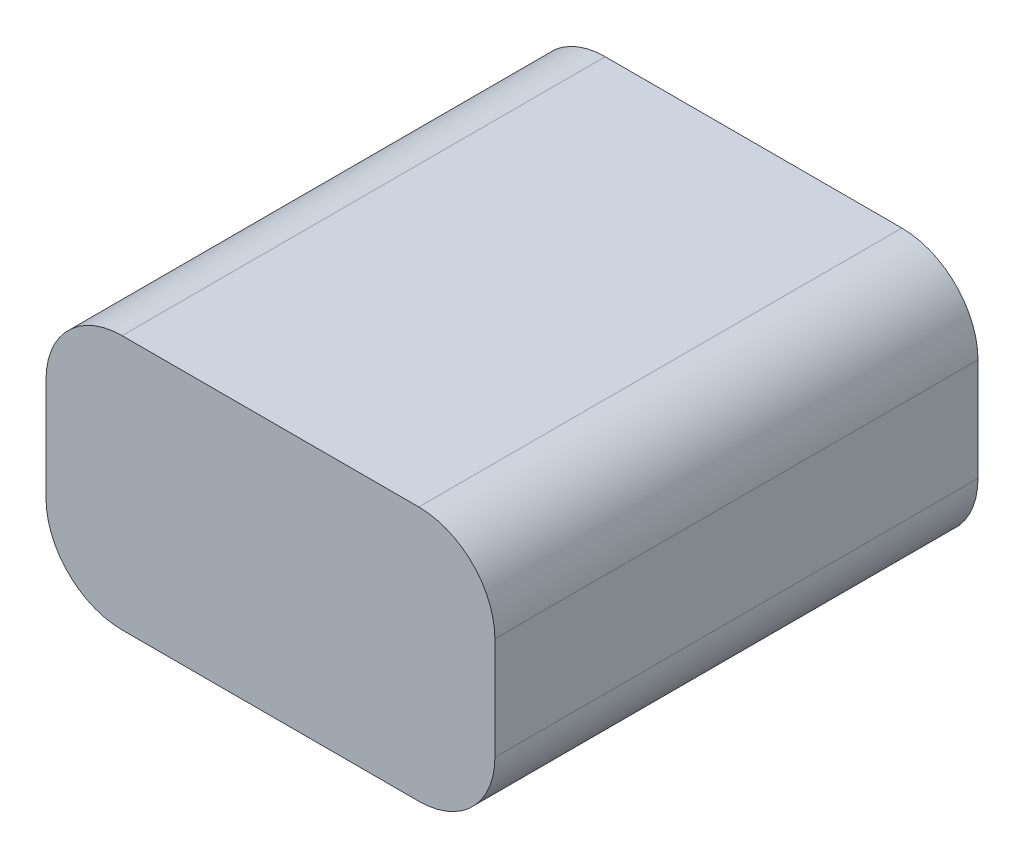
SolidWorks part; units mm, degrees
ref_plane "Front Plane" through (0, 0, 0) normal (0, 0, 1) x (1, 0, 0)
ref_plane "Top Plane" through (0, 0, 0) normal (0, 1, 0) x (1, 0, 0)
ref_plane "Right Plane" through (0, 0, 0) normal (1, 0, 0) x (0, 0, -1)
sketch "Sketch1" plane through (0, 0, 0) normal (0, 1, 0) x (1, 0, 0)
  line L1 (29.5, 31.75) -> (-29.5, 31.75)
  line L2 (29.5, 31.75) -> (29.5, -31.75)
  line L3 (29.5, -31.75) -> (-29.5, -31.75)
  line L4 (-29.5, 31.75) -> (-29.5, -31.75)
  line L5 (29.5, 31.75) -> (-29.5, -31.75) construction
  line L6 (29.5, -31.75) -> (-29.5, 31.75) construction
  point P0 (0, 0)
  dimension "D1" = 59
  dimension "D2" = 63.5
extrude "Boss-Extrude1" add sketch "Sketch1" along normal blind 33.5
fillet "Fillet1" radius 10 4 edges at (29.5, 33.5, 0) (29.5, 0, 0) (-29.5, 33.5, 0) (-29.5, 0, 0)
